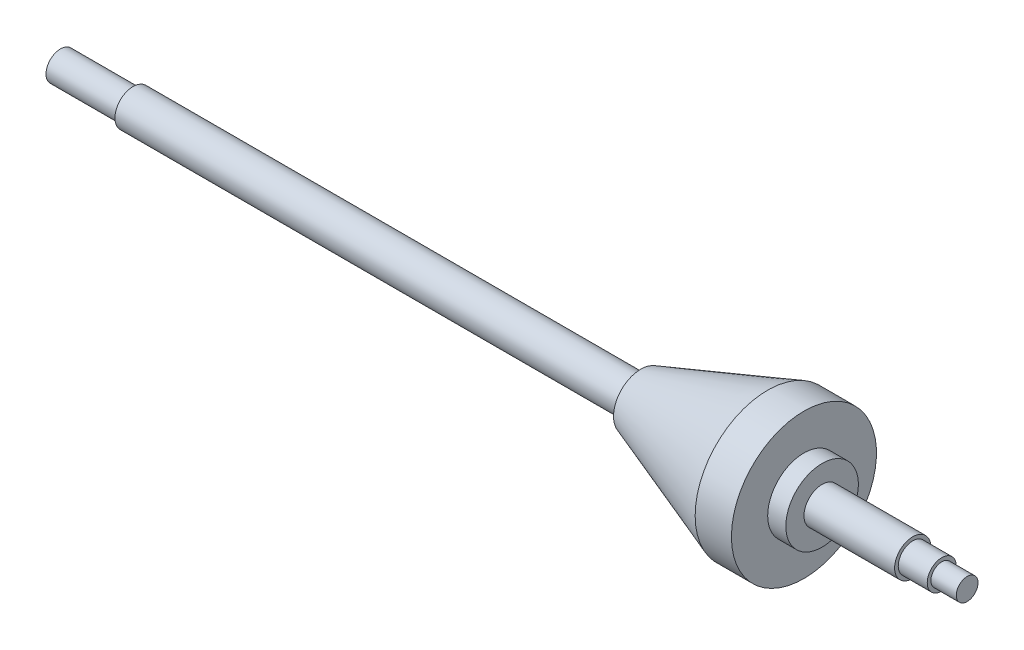
SolidWorks part; units mm, degrees
ref_plane "Front Plane" through (0, 0, 0) normal (0, 0, 1) x (1, 0, 0)
ref_plane "Top Plane" through (0, 0, 0) normal (0, 1, 0) x (1, 0, 0)
ref_plane "Right Plane" through (0, 0, 0) normal (1, 0, 0) x (0, 0, -1)
sketch "Sketch1" plane through (0, 0, 0) normal (0, 0, 1) x (1, 0, 0)
  line L0 (-132.6176, 0) -> (137.9118, 0) construction
  line L1 (-99.1471, 0) -> (-99.1471, 4)
  line L2 (-99.1471, 4) -> (-79.1471, 4)
  line L3 (-79.1471, 4) -> (-79.1471, 5)
  line L4 (-79.1471, 5) -> (60.8529, 5)
  line L5 (60.8529, 5) -> (60.8529, 7.5)
  line L6 (60.8529, 7.5) -> (95.8529, 20)
  line L7 (95.8529, 20) -> (105.8529, 20)
  line L8 (105.8529, 20) -> (105.8529, 10)
  line L9 (105.8529, 10) -> (110.8529, 10)
  line L10 (110.8529, 10) -> (110.8529, 5)
  line L11 (110.8529, 5) -> (135.8529, 5)
  line L12 (135.8529, 5) -> (135.8529, 4)
  line L13 (135.8529, 4) -> (143.8529, 4)
  line L14 (143.8529, 4) -> (143.8529, 3)
  line L15 (143.8529, 3) -> (150.8529, 3)
  line L16 (150.8529, 3) -> (150.8529, 0)
  line L17 (150.8529, 0) -> (-99.1471, 0)
  dimension "D1" = 45
  dimension "D2" = 38
  dimension "D3" = 30
  dimension "D4" = 5
  dimension "D5" = 185
  dimension "D6" = 10
  dimension "D7" = 45
  dimension "D8" = 20
  dimension "D9" = 8
  dimension "D10" = 10
  dimension "D11" = 15
  dimension "D12" = 6
  dimension "D13" = 8
  dimension "D14" = 10
  dimension "D15" = 20
  dimension "D16" = 40
revolve "Revolve1" add sketch "Sketch1" angle 360 about L0
